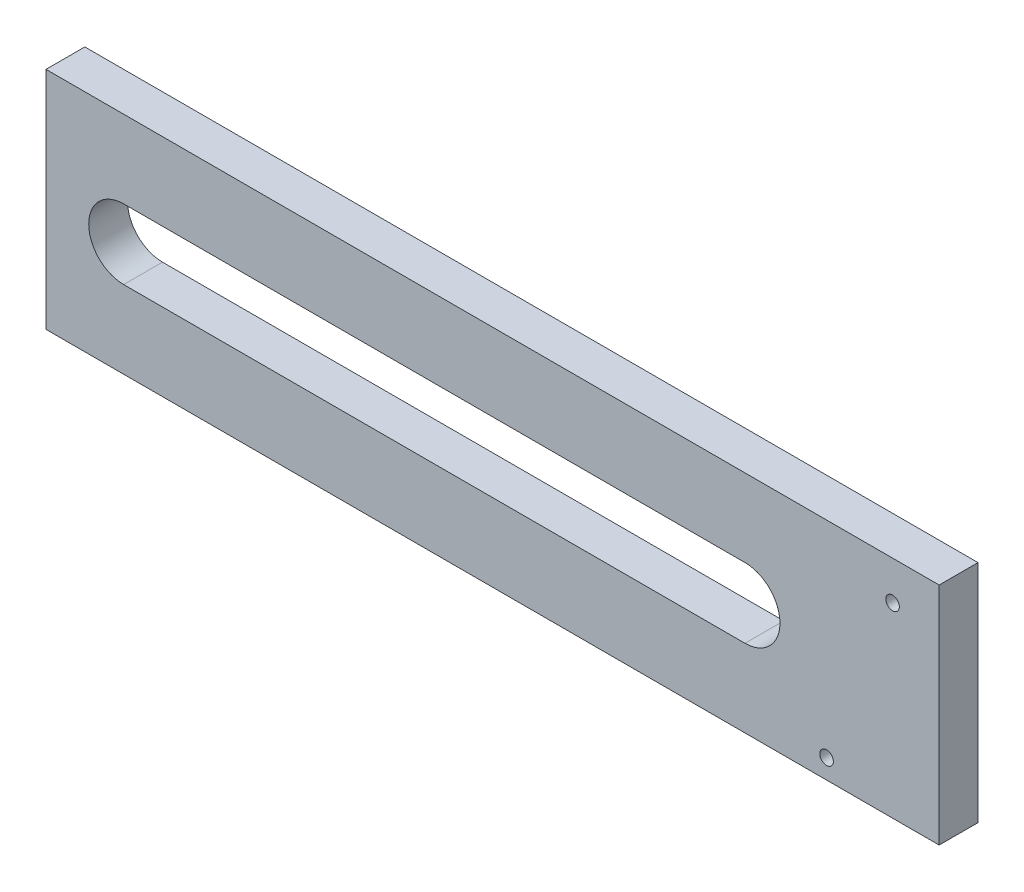
SolidWorks part; units mm, degrees
ref_plane "Plan de face" through (0, 0, 0) normal (0, 0, 1) x (1, 0, 0)
ref_plane "Plan de dessus" through (0, 0, 0) normal (0, 1, 0) x (1, 0, 0)
ref_plane "Plan de droite" through (0, 0, 0) normal (1, 0, 0) x (0, 0, -1)
sketch "Esquisse1" plane through (0, 0, 0) normal (0, 0, 1) x (1, 0, 0)
  line L1 (-134.2874, 29.9784) -> (95.7126, 29.9784)
  line L2 (-134.2874, 29.9784) -> (-134.2874, -28.0216)
  line L3 (-134.2874, -28.0216) -> (95.7126, -28.0216)
  line L4 (95.7126, 29.9784) -> (95.7126, -28.0216)
  line L5 (-114.2874, 9.9784) -> (45.7126, 9.9784)
  line L11 (45.7126, -8.0216) -> (-114.2874, -8.0216)
  arc A0 (45.7126, 9.9784) -> (45.7126, -8.0216) centre (45.7126, 0.9784) cw
  circle A1 centre (83.7126, 19.9784) radius 1.75
  arc A3 (-114.2874, 9.9784) -> (-114.2874, -8.0216) centre (-114.2874, 0.9784) ccw
  circle A4 centre (66.7126, -23.0216) radius 1.75
  dimension "D2" = 50
  dimension "D3" = 15
  dimension "D4" = 18
  dimension "D5" = 20
  dimension "D6" = 20
  dimension "D9" = 20
  dimension "D10" = 38
  dimension "D15" = 3.5
  dimension "D12" = 10
  dimension "D8" = 3.5
  dimension "D7" = 21
  dimension "D11" = 160
extrude "Boss.-Extru.1" add sketch "Esquisse1" along normal blind 10
